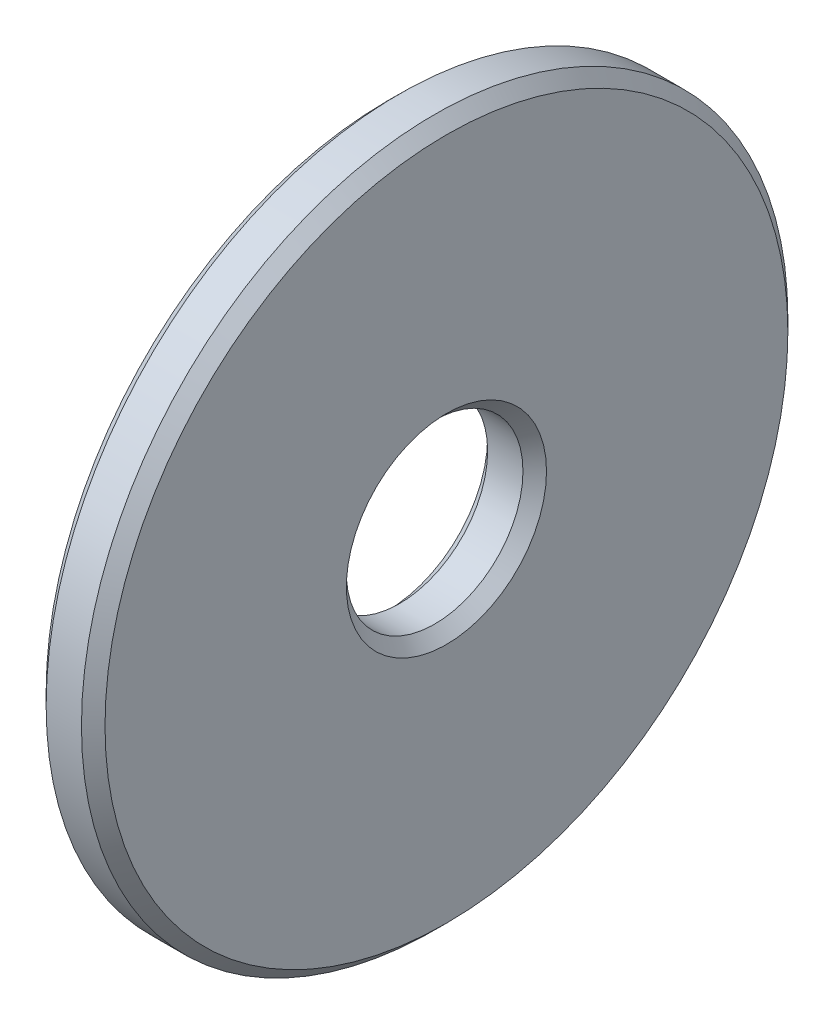
SolidWorks part; units mm, degrees
ref_plane "Front Plane" through (0, 0, 0) normal (0, 0, 1) x (1, 0, 0)
ref_plane "Top Plane" through (0, 0, 0) normal (0, 1, 0) x (1, 0, 0)
ref_plane "Right Plane" through (0, 0, 0) normal (1, 0, 0) x (0, 0, -1)
sketch "Sketch1" plane through (0, 0, 0) normal (0, 0, 1) x (1, 0, 0)
  line L0 (0, 5.8) -> (0, 1.7)
  line L1 (0, 1.7) -> (0.2, 1.5)
  line L2 (0.2, 1.5) -> (0.8, 1.5)
  line L3 (0.8, 1.5) -> (1, 1.7)
  line L4 (1, 1.7) -> (1, 5.8)
  line L5 (1, 5.8) -> (0.8, 6)
  line L6 (0.8, 6) -> (0.2, 6)
  line L7 (0.2, 6) -> (0, 5.8)
  line L8 (0, 0) -> (1, 0) construction
revolve "Revolve1" add sketch "Sketch1" angle 360 about L8
